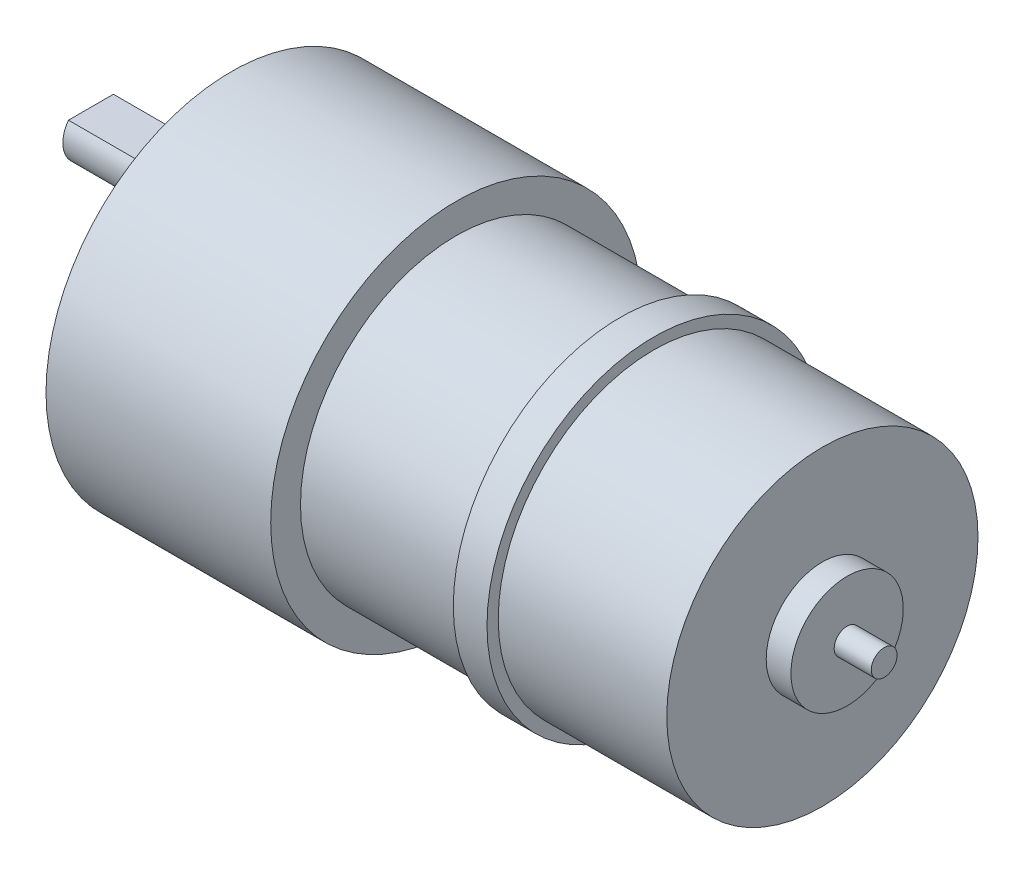
SolidWorks part; units mm, degrees
ref_plane "Front Plane" through (0, 0, 0) normal (0, 0, 1) x (1, 0, 0)
ref_plane "Top Plane" through (0, 0, 0) normal (0, 1, 0) x (1, 0, 0)
ref_plane "Right Plane" through (0, 0, 0) normal (1, 0, 0) x (0, 0, -1)
sketch "Sketch1" plane through (0, 0, 0) normal (0, 0, 1) x (1, 0, 0)
  line L1 (0, 0) -> (20, 0)
  line L2 (0, 0) -> (0, 16.5)
  line L3 (0, 16.5) -> (20, 16.5)
  line L4 (20, 0) -> (20, 16.5)
  line L5 (20, 0) -> (52.6, 0)
  line L6 (20, 0) -> (20, 13.85)
  line L7 (20, 13.85) -> (52.6, 13.85)
  line L8 (52.6, 0) -> (52.6, 13.85)
  line L9 (34.6, 0) -> (37.6, 0)
  line L10 (34.6, 0) -> (34.6, 14.85)
  line L11 (34.6, 14.85) -> (37.6, 14.85)
  line L12 (37.6, 0) -> (37.6, 14.85)
  line L13 (52.6, 0) -> (54.8, 0)
  line L14 (52.6, 0) -> (52.6, 5)
  line L15 (52.6, 5) -> (54.8, 5)
  line L16 (54.8, 0) -> (54.8, 5)
  line L17 (54.8, 0) -> (58.1, 0)
  line L18 (54.8, 0) -> (54.8, 1.15)
  line L19 (54.8, 1.15) -> (58.1, 1.15)
  line L20 (58.1, 0) -> (58.1, 1.15)
  dimension "D1" = 20
  dimension "D2" = 32.6
  dimension "D3" = 5.5
  dimension "D4" = 2.2
  dimension "D5" = 15
  dimension "D6" = 3
  dimension "D7" = 13.85
  dimension "D8" = 5
  dimension "D9" = 1.15
  dimension "D10" = 1
  dimension "D11" = 16.5
revolve "Revolve1" add sketch "Sketch1" angle 360 about L1
sketch "Sketch3" plane through (0, 0, 0) normal (0, 0, 1) x (1, 0, 0)
  line L0 (-12.5, 6) -> (0, 6)
  line L2 (-12.5, 6) -> (-2, 6)
  line L3 (-12.5, 6) -> (-12.5, 8.5)
  line L4 (-12.5, 8.5) -> (-2, 8.5)
  line L5 (-2, 6) -> (-2, 8.5)
  line L6 (0, 6) -> (-2, 6)
  line L7 (0, 6) -> (0, 11)
  line L8 (0, 11) -> (-2, 11)
  line L9 (-2, 6) -> (-2, 11)
  dimension "D1" = 6
  dimension "D2" = 2.5
  dimension "D3" = 5
  dimension "D4" = 12.5
  dimension "D5" = 10.5
revolve "Revolve2" add sketch "Sketch3" angle 360 about L0
sketch "Sketch4" plane through (-12.5, 0, 0) normal (-1, 0, 0) x (0, 0, 1)
  line L0 (-2, 7.5) -> (2, 7.5)
  line L1 (0, 7.5) -> (0, 3.5) construction
  circle A1 centre (0, 6) radius 2.5
  circle A2 centre (0, 6) radius 2.5
  circle M4 centre (0, 6) radius 2.5
  dimension "D2" = 4
  dimension "D1" = 0
extrude "Cut-Extrude1" cut sketch "Sketch4" against normal blind 8 contours L0 M4
